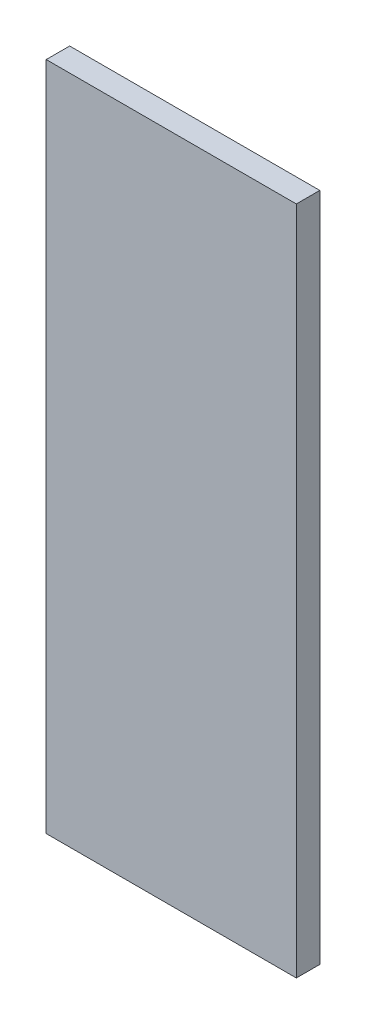
SolidWorks part; units mm, degrees
ref_plane "Front Plane" through (0, 0, 0) normal (0, 0, 1) x (1, 0, 0)
ref_plane "Top Plane" through (0, 0, 0) normal (0, 1, 0) x (1, 0, 0)
ref_plane "Right Plane" through (0, 0, 0) normal (1, 0, 0) x (0, 0, -1)
sketch "Sketch1" plane through (0, 0, 0) normal (0, 1, 0) x (1, 0, 0)
  line L1 (0, 0) -> (203.2, 0)
  line L2 (0, 0) -> (0, 19.05)
  line L3 (0, 19.05) -> (203.2, 19.05)
  line L4 (203.2, 0) -> (203.2, 19.05)
  dimension "D1" = 19.05
  dimension "D2" = 203.2
extrude "Boss-Extrude1" add sketch "Sketch1" along normal blind 544.576
